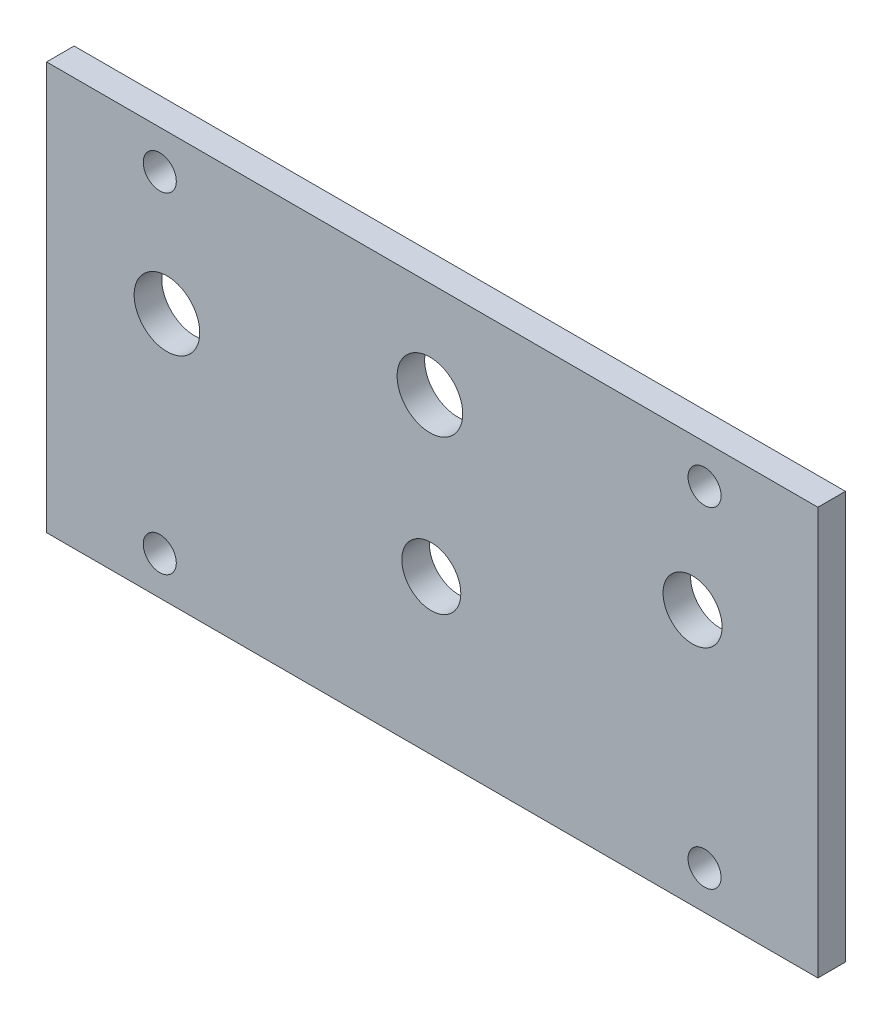
SolidWorks part; units mm, degrees
ref_plane "Front Plane" through (0, 0, 0) normal (0, 0, 1) x (1, 0, 0)
ref_plane "Top Plane" through (0, 0, 0) normal (0, 1, 0) x (1, 0, 0)
ref_plane "Right Plane" through (0, 0, 0) normal (1, 0, 0) x (0, 0, -1)
sketch "Sketch1" plane through (0, 0, 0) normal (0, 0, 1) x (1, 0, 0)
  line L1 (35.7259, 6.6675) -> (124.6259, 6.6675)
  line L2 (35.7259, 6.6675) -> (35.7259, 53.6575)
  line L3 (35.7259, 53.6575) -> (124.6259, 53.6575)
  line L4 (124.6259, 6.6675) -> (124.6259, 53.6575)
  line L15 (37.5111, 35.7405) -> (35.7259, 35.7405)
  line L16 (80.1688, 50.7365) -> (80.1759, 53.6575) construction
  line L17 (122.8407, 30.1625) -> (124.6259, 30.1625) construction
  line L18 (80.1688, 9.5885) -> (80.1759, 6.6675)
  circle A1 centre (48.7744, 49.2125) radius 1.905
  circle A3 centre (111.5631, 49.2125) radius 1.905
  circle A5 centre (48.7744, 11.1125) radius 1.905
  circle A7 centre (111.5632, 11.1125) radius 1.905
  arc A543 (46.201, 35.4588) -> (53.001, 35.4588) centre (49.601, 35.4588) ccw construction
  arc A544 (53.001, 35.4588) -> (46.201, 35.4588) centre (49.601, 35.4588) ccw construction
  arc A545 (83.4694, 24.4521) -> (76.6694, 24.4521) centre (80.0694, 24.4521) ccw construction
  arc A546 (76.6694, 24.4521) -> (83.4694, 24.4521) centre (80.0694, 24.4521) ccw construction
  arc A547 (106.7809, 36.1849) -> (113.5809, 36.1849) centre (110.1809, 36.1849) ccw construction
  arc A548 (113.5809, 36.1849) -> (106.7809, 36.1849) centre (110.1809, 36.1849) ccw construction
  arc A549 (76.5088, 42.5096) -> (83.3088, 42.5096) centre (79.9088, 42.5096) ccw construction
  arc A550 (83.3088, 42.5096) -> (76.5088, 42.5096) centre (79.9088, 42.5096) ccw construction
  arc A559 (46.201, 35.4588) -> (53.001, 35.4588) centre (49.601, 35.4588) ccw construction
  arc A560 (53.001, 35.4588) -> (46.201, 35.4588) centre (49.601, 35.4588) ccw construction
  arc A561 (83.4694, 24.4521) -> (76.6694, 24.4521) centre (80.0694, 24.4521) ccw
  arc A562 (76.6694, 24.4521) -> (83.4694, 24.4521) centre (80.0694, 24.4521) ccw
  arc A563 (106.7809, 36.1849) -> (113.5809, 36.1849) centre (110.1809, 36.1849) ccw
  arc A564 (113.5809, 36.1849) -> (106.7809, 36.1849) centre (110.1809, 36.1849) ccw
  arc A565 (76.5088, 42.5096) -> (83.3088, 42.5096) centre (79.9088, 42.5096) ccw construction
  arc A566 (83.3088, 42.5096) -> (76.5088, 42.5096) centre (79.9088, 42.5096) ccw construction
  arc A567 (53.382, 35.4588) -> (45.82, 35.4588) centre (49.601, 35.4588) ccw
  arc A568 (45.82, 35.4588) -> (53.382, 35.4588) centre (49.601, 35.4588) ccw
  arc A569 (83.6898, 42.5096) -> (76.1278, 42.5096) centre (79.9088, 42.5096) ccw
  arc A570 (76.1278, 42.5096) -> (83.6898, 42.5096) centre (79.9088, 42.5096) ccw
  arc A571 (76.2884, 24.4521) -> (83.8504, 24.4521) centre (80.0694, 24.4521) ccw construction
  arc A572 (83.8504, 24.4521) -> (76.2884, 24.4521) centre (80.0694, 24.4521) ccw construction
  arc A573 (113.9619, 36.1849) -> (106.3999, 36.1849) centre (110.1809, 36.1849) ccw construction
  arc A574 (106.3999, 36.1849) -> (113.9619, 36.1849) centre (110.1809, 36.1849) ccw construction
  dimension "D3" = 0.381
  dimension "D1" = 46.99
  dimension "D2" = 88.9
extrude "Boss-Extrude1" add sketch "Sketch1" along normal blind 3.175
